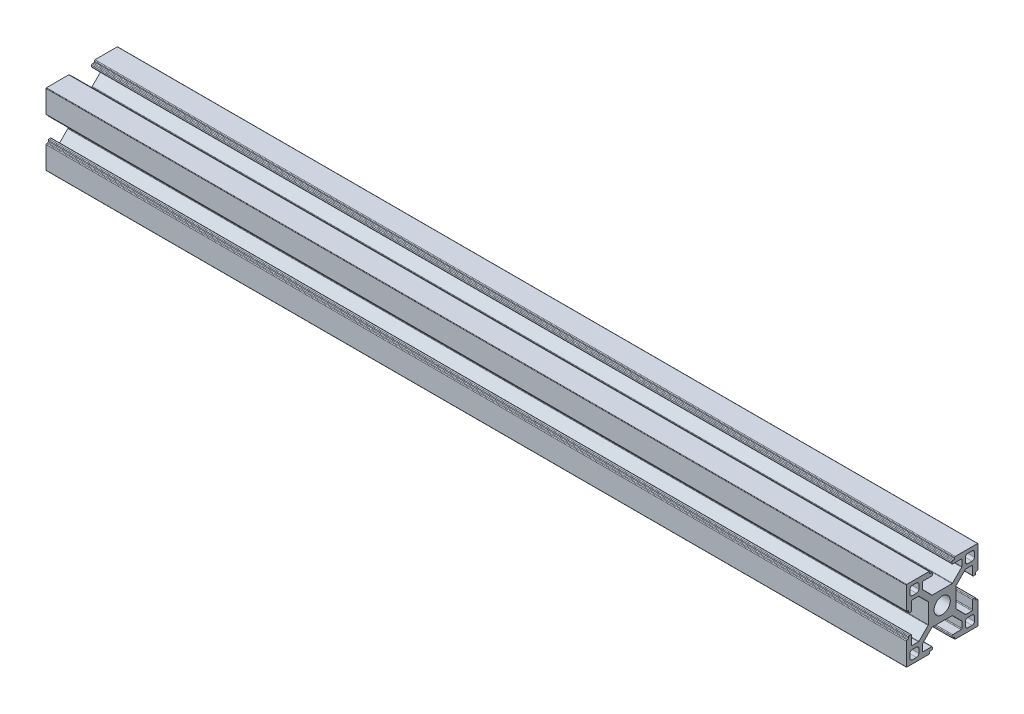
SolidWorks part; units mm, degrees
ref_plane "前视基准面" through (0, 0, 0) normal (0, 0, 1) x (1, 0, 0)
ref_plane "上视基准面" through (0, 0, 0) normal (0, 1, 0) x (1, 0, 0)
ref_plane "右视基准面" through (0, 0, 0) normal (1, 0, 0) x (0, 0, -1)
sketch "草图1" plane through (0, 0, 0) normal (0, 0, 1) x (1, 0, 0)
  line L0 (0, 0) -> (360, 0)
  dimension "D1" = 360
other "3030a 默认<按加工>(1)"
ref_plane "基准面1" through (0, 0, 0) normal (1, 0, 0) x (0, 1, 0)
sketch "草图11" plane through (0, 0, 0) normal (1, 0, 0) x (0, 1, 0)
  line L82 (0, 5.8) -> (-4.1201, 5.8)
  line L83 (-4.3322, 5.8879) -> (-8.1621, 9.7178)
  line L84 (-8.25, 9.9299) -> (-8.25, 12.5)
  line L85 (-7.95, 12.8) -> (-4.4, 12.8)
  line L86 (-4.1, 13.1) -> (-4.1, 13.7)
  line L87 (-4.4, 14) -> (-4.9, 14)
  line L88 (-5.2, 14.3) -> (-5.2, 14.7)
  line L89 (-5.5, 15) -> (-14.8, 15)
  line L90 (-15, 14.8) -> (-15, 5.5)
  line L91 (-14.7, 5.2) -> (-14.3, 5.2)
  line L92 (-14, 4.9) -> (-14, 4.4)
  line L93 (-13.7, 4.1) -> (-13.1, 4.1)
  line L94 (-12.8, 4.4) -> (-12.8, 7.95)
  line L95 (-12.5, 8.25) -> (-9.9299, 8.25)
  line L96 (-9.7178, 8.1621) -> (-5.8879, 4.3322)
  line L97 (-5.8, 4.1201) -> (-5.8, 0)
  line L98 (-5.8, 0) -> (-5.8, -4.1201)
  line L99 (-5.8879, -4.3322) -> (-9.7178, -8.1621)
  line L100 (-9.9299, -8.25) -> (-12.5, -8.25)
  line L101 (-12.8, -7.95) -> (-12.8, -4.4)
  line L102 (-13.1, -4.1) -> (-13.7, -4.1)
  line L103 (-14, -4.4) -> (-14, -4.9)
  line L104 (-14.3, -5.2) -> (-14.7, -5.2)
  line L105 (-15, -5.5) -> (-15, -14.8)
  line L106 (-14.8, -15) -> (-5.5, -15)
  line L107 (-5.2, -14.7) -> (-5.2, -14.3)
  line L108 (-4.9, -14) -> (-4.4, -14)
  line L109 (-4.1, -13.7) -> (-4.1, -13.1)
  line L110 (-4.4, -12.8) -> (-7.95, -12.8)
  line L111 (-8.25, -12.5) -> (-8.25, -9.9299)
  line L112 (-8.1621, -9.7178) -> (-4.3322, -5.8879)
  line L113 (-4.1201, -5.8) -> (0, -5.8)
  line L114 (0, -5.8) -> (4.1201, -5.8)
  line L115 (4.3322, -5.8879) -> (8.1621, -9.7178)
  line L116 (8.25, -9.9299) -> (8.25, -12.5)
  line L117 (7.95, -12.8) -> (4.4, -12.8)
  line L118 (4.1, -13.1) -> (4.1, -13.7)
  line L119 (4.4, -14) -> (4.9, -14)
  line L120 (5.2, -14.3) -> (5.2, -14.7)
  line L121 (5.5, -15) -> (14.8, -15)
  line L122 (15, -14.8) -> (15, -5.5)
  line L123 (14.7, -5.2) -> (14.3, -5.2)
  line L124 (14, -4.9) -> (14, -4.4)
  line L125 (13.7, -4.1) -> (13.1, -4.1)
  line L126 (12.8, -4.4) -> (12.8, -7.95)
  line L127 (12.5, -8.25) -> (9.9299, -8.25)
  line L128 (9.7178, -8.1621) -> (5.8879, -4.3322)
  line L129 (5.8, -4.1201) -> (5.8, 0)
  line L130 (5.8, 0) -> (5.8, 4.1201)
  line L131 (5.8879, 4.3322) -> (9.8056, 8.25)
  line L132 (9.8056, 8.25) -> (12.5, 8.25)
  line L133 (12.8, 7.95) -> (12.8, 4.4)
  line L134 (13.1, 4.1) -> (13.7, 4.1)
  line L135 (14, 4.4) -> (14, 4.9)
  line L136 (14.3, 5.2) -> (14.7, 5.2)
  line L137 (15, 5.5) -> (15, 14.8)
  line L138 (14.8, 15) -> (5.5, 15)
  line L139 (5.2, 14.7) -> (5.2, 14.3)
  line L140 (4.9, 14) -> (4.4, 14)
  line L141 (4.1, 13.7) -> (4.1, 13.1)
  line L142 (4.4, 12.8) -> (7.95, 12.8)
  line L143 (8.25, 12.5) -> (8.25, 9.9299)
  line L144 (8.1621, 9.7178) -> (4.3322, 5.8879)
  line L145 (4.1201, 5.8) -> (0, 5.8)
  line L146 (-10.75, -13.5) -> (-12.5, -13.5)
  line L147 (-13.5, -12.5) -> (-13.5, -10.75)
  line L148 (-12.5, -9.75) -> (-10.75, -9.75)
  line L149 (-9.75, -10.75) -> (-9.75, -12.5)
  line L150 (10.75, -13.5) -> (12.5, -13.5)
  line L151 (13.5, -12.5) -> (13.5, -10.75)
  line L152 (12.5, -9.75) -> (10.75, -9.75)
  line L153 (9.75, -10.75) -> (9.75, -12.5)
  line L154 (-10.75, 13.5) -> (-12.5, 13.5)
  line L155 (-13.5, 12.5) -> (-13.5, 10.75)
  line L156 (-12.5, 9.75) -> (-10.75, 9.75)
  line L157 (-9.75, 10.75) -> (-9.75, 12.5)
  line L158 (10.75, 13.5) -> (12.5, 13.5)
  line L159 (13.5, 12.5) -> (13.5, 10.75)
  line L160 (12.5, 9.75) -> (10.75, 9.75)
  line L161 (9.75, 10.75) -> (9.75, 12.5)
  circle A76 centre (0, 0) radius 3.4
  arc A77 (-4.3322, 5.8879) -> (-4.1201, 5.8) centre (-4.1201, 6.1) ccw
  arc A78 (-8.25, 9.9299) -> (-8.1621, 9.7178) centre (-7.95, 9.9299) ccw
  arc A79 (-7.95, 12.8) -> (-8.25, 12.5) centre (-7.95, 12.5) ccw
  arc A80 (-4.4, 12.8) -> (-4.1, 13.1) centre (-4.4, 13.1) ccw
  arc A81 (-4.1, 13.7) -> (-4.4, 14) centre (-4.4, 13.7) ccw
  arc A82 (-5.2, 14.3) -> (-4.9, 14) centre (-4.9, 14.3) ccw
  arc A83 (-5.2, 14.7) -> (-5.5, 15) centre (-5.5, 14.7) ccw
  arc A84 (-14.8, 15) -> (-15, 14.8) centre (-14.8, 14.8) ccw
  arc A85 (-15, 5.5) -> (-14.7, 5.2) centre (-14.7, 5.5) ccw
  arc A86 (-14, 4.9) -> (-14.3, 5.2) centre (-14.3, 4.9) ccw
  arc A87 (-14, 4.4) -> (-13.7, 4.1) centre (-13.7, 4.4) ccw
  arc A88 (-13.1, 4.1) -> (-12.8, 4.4) centre (-13.1, 4.4) ccw
  arc A89 (-12.5, 8.25) -> (-12.8, 7.95) centre (-12.5, 7.95) ccw
  arc A90 (-9.7178, 8.1621) -> (-9.9299, 8.25) centre (-9.9299, 7.95) ccw
  arc A91 (-5.8, 4.1201) -> (-5.8879, 4.3322) centre (-6.1, 4.1201) ccw
  arc A92 (-5.8879, -4.3322) -> (-5.8, -4.1201) centre (-6.1, -4.1201) ccw
  arc A93 (-9.9299, -8.25) -> (-9.7178, -8.1621) centre (-9.9299, -7.95) ccw
  arc A94 (-12.8, -7.95) -> (-12.5, -8.25) centre (-12.5, -7.95) ccw
  arc A95 (-12.8, -4.4) -> (-13.1, -4.1) centre (-13.1, -4.4) ccw
  arc A96 (-13.7, -4.1) -> (-14, -4.4) centre (-13.7, -4.4) ccw
  arc A97 (-14.3, -5.2) -> (-14, -4.9) centre (-14.3, -4.9) ccw
  arc A98 (-14.7, -5.2) -> (-15, -5.5) centre (-14.7, -5.5) ccw
  arc A99 (-15, -14.8) -> (-14.8, -15) centre (-14.8, -14.8) ccw
  arc A100 (-5.5, -15) -> (-5.2, -14.7) centre (-5.5, -14.7) ccw
  arc A101 (-4.9, -14) -> (-5.2, -14.3) centre (-4.9, -14.3) ccw
  arc A102 (-4.4, -14) -> (-4.1, -13.7) centre (-4.4, -13.7) ccw
  arc A103 (-4.1, -13.1) -> (-4.4, -12.8) centre (-4.4, -13.1) ccw
  arc A104 (-8.25, -12.5) -> (-7.95, -12.8) centre (-7.95, -12.5) ccw
  arc A105 (-8.1621, -9.7178) -> (-8.25, -9.9299) centre (-7.95, -9.9299) ccw
  arc A106 (-4.1201, -5.8) -> (-4.3322, -5.8879) centre (-4.1201, -6.1) ccw
  arc A107 (4.3322, -5.8879) -> (4.1201, -5.8) centre (4.1201, -6.1) ccw
  arc A108 (8.25, -9.9299) -> (8.1621, -9.7178) centre (7.95, -9.9299) ccw
  arc A109 (7.95, -12.8) -> (8.25, -12.5) centre (7.95, -12.5) ccw
  arc A110 (4.4, -12.8) -> (4.1, -13.1) centre (4.4, -13.1) ccw
  arc A111 (4.1, -13.7) -> (4.4, -14) centre (4.4, -13.7) ccw
  arc A112 (5.2, -14.3) -> (4.9, -14) centre (4.9, -14.3) ccw
  arc A113 (5.2, -14.7) -> (5.5, -15) centre (5.5, -14.7) ccw
  arc A114 (14.8, -15) -> (15, -14.8) centre (14.8, -14.8) ccw
  arc A115 (15, -5.5) -> (14.7, -5.2) centre (14.7, -5.5) ccw
  arc A116 (14, -4.9) -> (14.3, -5.2) centre (14.3, -4.9) ccw
  arc A117 (14, -4.4) -> (13.7, -4.1) centre (13.7, -4.4) ccw
  arc A118 (13.1, -4.1) -> (12.8, -4.4) centre (13.1, -4.4) ccw
  arc A119 (12.5, -8.25) -> (12.8, -7.95) centre (12.5, -7.95) ccw
  arc A120 (9.7178, -8.1621) -> (9.9299, -8.25) centre (9.9299, -7.95) ccw
  arc A121 (5.8, -4.1201) -> (5.8879, -4.3322) centre (6.1, -4.1201) ccw
  arc A122 (5.8879, 4.3322) -> (5.8, 4.1201) centre (6.1, 4.1201) ccw
  arc A123 (12.8, 7.95) -> (12.5, 8.25) centre (12.5, 7.95) ccw
  arc A124 (12.8, 4.4) -> (13.1, 4.1) centre (13.1, 4.4) ccw
  arc A125 (13.7, 4.1) -> (14, 4.4) centre (13.7, 4.4) ccw
  arc A126 (14.3, 5.2) -> (14, 4.9) centre (14.3, 4.9) ccw
  arc A127 (14.7, 5.2) -> (15, 5.5) centre (14.7, 5.5) ccw
  arc A128 (15, 14.8) -> (14.8, 15) centre (14.8, 14.8) ccw
  arc A129 (5.5, 15) -> (5.2, 14.7) centre (5.5, 14.7) ccw
  arc A130 (4.9, 14) -> (5.2, 14.3) centre (4.9, 14.3) ccw
  arc A131 (4.4, 14) -> (4.1, 13.7) centre (4.4, 13.7) ccw
  arc A132 (4.1, 13.1) -> (4.4, 12.8) centre (4.4, 13.1) ccw
  arc A133 (8.25, 12.5) -> (7.95, 12.8) centre (7.95, 12.5) ccw
  arc A134 (8.1621, 9.7178) -> (8.25, 9.9299) centre (7.95, 9.9299) ccw
  arc A135 (4.1201, 5.8) -> (4.3322, 5.8879) centre (4.1201, 6.1) ccw
  arc A136 (-10.75, -13.5) -> (-9.75, -12.5) centre (-10.75, -12.5) ccw
  arc A137 (-13.5, -12.5) -> (-12.5, -13.5) centre (-12.5, -12.5) ccw
  arc A138 (-12.5, -9.75) -> (-13.5, -10.75) centre (-12.5, -10.75) ccw
  arc A139 (-9.75, -10.75) -> (-10.75, -9.75) centre (-10.75, -10.75) ccw
  arc A140 (9.75, -12.5) -> (10.75, -13.5) centre (10.75, -12.5) ccw
  arc A141 (12.5, -13.5) -> (13.5, -12.5) centre (12.5, -12.5) ccw
  arc A142 (13.5, -10.75) -> (12.5, -9.75) centre (12.5, -10.75) ccw
  arc A143 (10.75, -9.75) -> (9.75, -10.75) centre (10.75, -10.75) ccw
  arc A144 (-9.75, 12.5) -> (-10.75, 13.5) centre (-10.75, 12.5) ccw
  arc A145 (-12.5, 13.5) -> (-13.5, 12.5) centre (-12.5, 12.5) ccw
  arc A146 (-13.5, 10.75) -> (-12.5, 9.75) centre (-12.5, 10.75) ccw
  arc A147 (-10.75, 9.75) -> (-9.75, 10.75) centre (-10.75, 10.75) ccw
  arc A148 (10.75, 13.5) -> (9.75, 12.5) centre (10.75, 12.5) ccw
  arc A149 (13.5, 12.5) -> (12.5, 13.5) centre (12.5, 12.5) ccw
  arc A150 (12.5, 9.75) -> (13.5, 10.75) centre (12.5, 10.75) ccw
  arc A151 (9.75, 10.75) -> (10.75, 9.75) centre (10.75, 10.75) ccw
  point P0 (0, 0)
